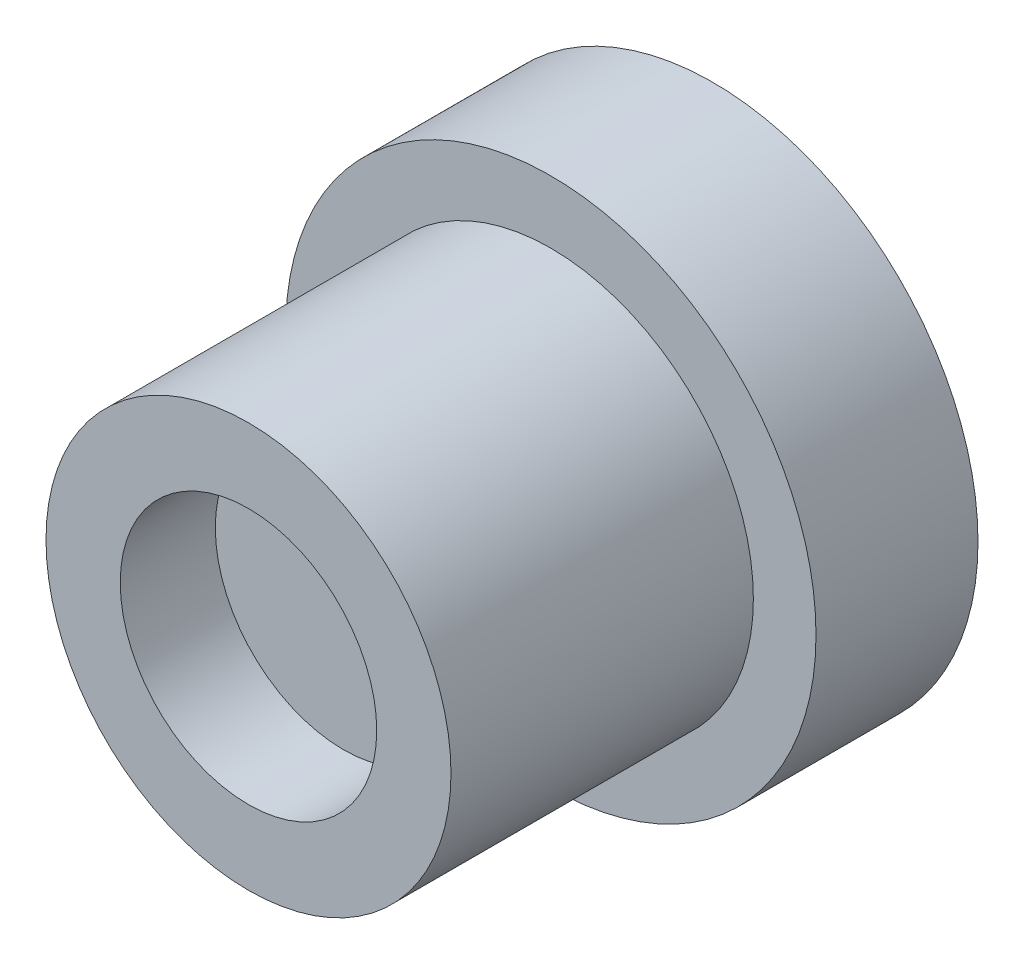
SolidWorks part; units mm, degrees
ref_plane "Front Plane" through (0, 0, 0) normal (0, 0, 1) x (1, 0, 0)
ref_plane "Top Plane" through (0, 0, 0) normal (0, 1, 0) x (1, 0, 0)
ref_plane "Right Plane" through (0, 0, 0) normal (1, 0, 0) x (0, 0, -1)
sketch "Sketch1" plane through (0, 0, 0) normal (0, 0, 1) x (1, 0, 0)
  circle A1 centre (0, 0) radius 4.91
  dimension "D1" = 9.82
extrude "Boss-Extrude1" add sketch "Sketch1" along normal blind 3 contours A1
sketch "Sketch4" plane through (0, 0, 3) normal (0, 0, 1) x (1, 0, 0)
  circle A0 centre (0, 0) radius 3.75
  dimension "D1" = 7.5
extrude "Boss-Extrude3" add sketch "Sketch4" along normal blind 3.84
sketch "Sketch2" plane through (0, 0, 6.84) normal (0, 0, 1) x (1, 0, 0)
  circle A0 centre (0, 0) radius 2.375
  circle A1 centre (0, 0) radius 3.75
  circle A2 centre (0, 0) radius 3.75 construction
  dimension "D2" = 4.75
extrude "Boss-Extrude2" add sketch "Sketch2" along normal blind 1.76
